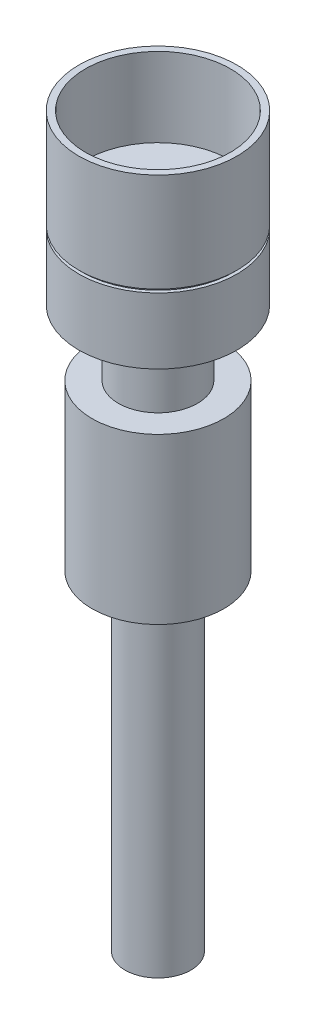
SolidWorks part; units mm, degrees
ref_plane "前视" through (0, 0, 0) normal (0, 0, 1) x (1, 0, 0)
ref_plane "上视" through (0, 0, 0) normal (0, 1, 0) x (1, 0, 0)
ref_plane "右视" through (0, 0, 0) normal (1, 0, 0) x (0, 0, -1)
sketch "草图1" plane through (0, 0, 0) normal (0, 1, 0) x (1, 0, 0)
  circle A0 centre (0, 0) radius 10
  dimension "D1" = 20
extrude "凸台-拉伸1" add sketch "草图1" along normal blind 25
sketch "草图2" plane through (0, 0, 0) normal (0, -1, 0) x (1, 0, 0)
  circle A0 centre (0, 0) radius 5
  dimension "D1" = 10
extrude "凸台-拉伸2" add sketch "草图2" along normal blind 50
sketch "草图3" plane through (0, 25, 0) normal (0, 1, 0) x (1, 0, 0)
  circle A0 centre (0, 0) radius 6
  dimension "D1" = 12
extrude "凸台-拉伸3" add sketch "草图3" along normal blind 10
sketch "草图4" plane through (0, 35, 0) normal (0, 1, 0) x (1, 0, 0)
  circle A0 centre (0, 0) radius 12
  dimension "D1" = 24
extrude "凸台-拉伸4" add sketch "草图4" along normal blind 10
sketch "草图5" plane through (0, 45, 0) normal (0, 1, 0) x (1, 0, 0)
  circle A0 centre (0, 0) radius 12
  dimension "D1" = 24
extrude "凸台-拉伸5" add sketch "草图5" along normal blind 15 from offset 0.5 separate body
sketch "草图6" plane through (0, 45, 0) normal (0, 1, 0) x (1, 0, 0)
  circle A0 centre (0, 0) radius 11.5
  dimension "D1" = 23
extrude "凸台-拉伸6" add sketch "草图6" along normal blind 1
sketch "草图7" plane through (0, 60.5, 0) normal (0, 1, 0) x (1, 0, 0)
  circle A0 centre (0, 0) radius 11
  dimension "D1" = 22
extrude "切除-拉伸1" cut sketch "草图7" against normal blind 12
